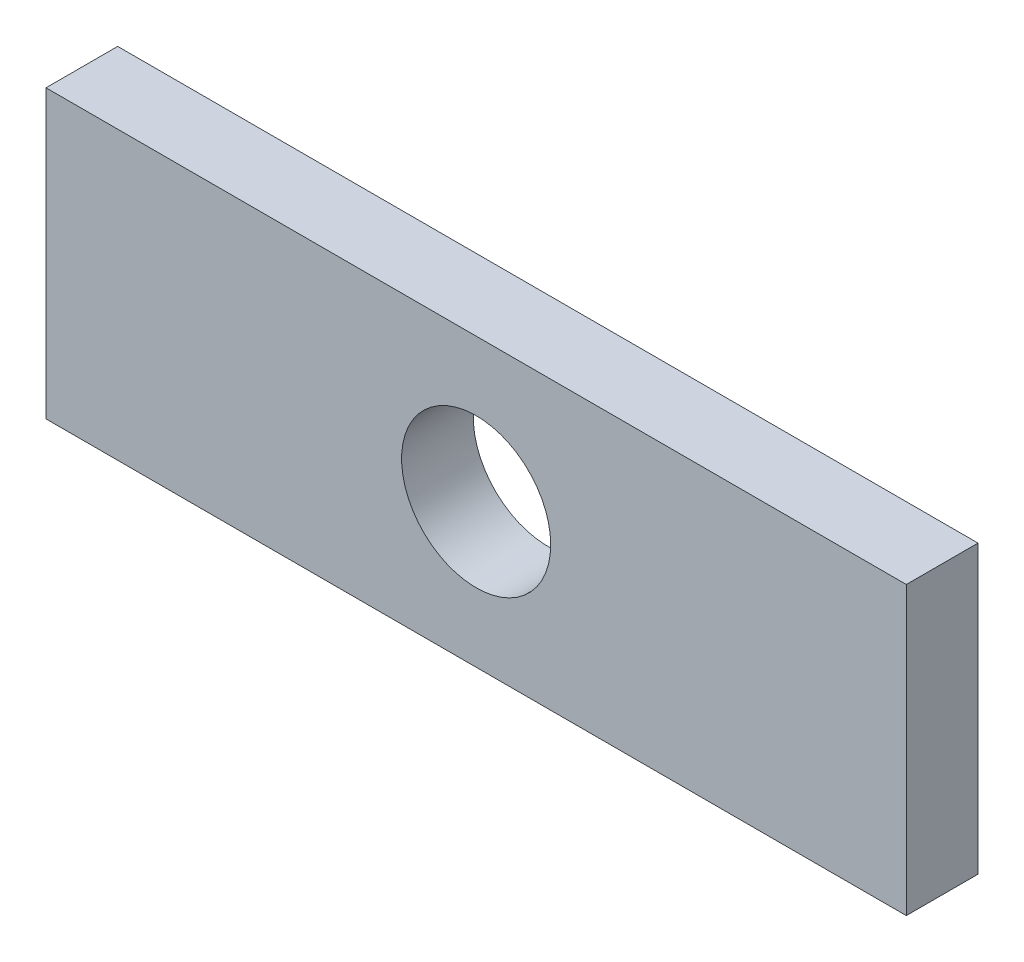
SolidWorks part; units mm, degrees
ref_plane "Front Plane" through (0, 0, 0) normal (0, 0, 1) x (1, 0, 0)
ref_plane "Top Plane" through (0, 0, 0) normal (0, 1, 0) x (1, 0, 0)
ref_plane "Right Plane" through (0, 0, 0) normal (1, 0, 0) x (0, 0, -1)
sketch "Sketch1" plane through (0, 0, 0) normal (0, 0, 1) x (1, 0, 0)
  line L1 (-19.05, 6.35) -> (19.05, 6.35)
  line L2 (-19.05, 6.35) -> (-19.05, -6.35)
  line L3 (-19.05, -6.35) -> (19.05, -6.35)
  line L4 (19.05, 6.35) -> (19.05, -6.35)
  circle A0 centre (0, 0) radius 3.302
  dimension "D5" = 6.604
  dimension "D1" = 38.1
  dimension "D2" = 19.05
  dimension "D3" = 12.7
  dimension "D4" = 6.35
extrude "Extrude1" add sketch "Sketch1" along normal blind 3.175
equation "\"D2@Sketch1\" = \"D1@Sketch1\" / 2"
equation "\"D4@Sketch1\" = \"D3@Sketch1\" / 2"
